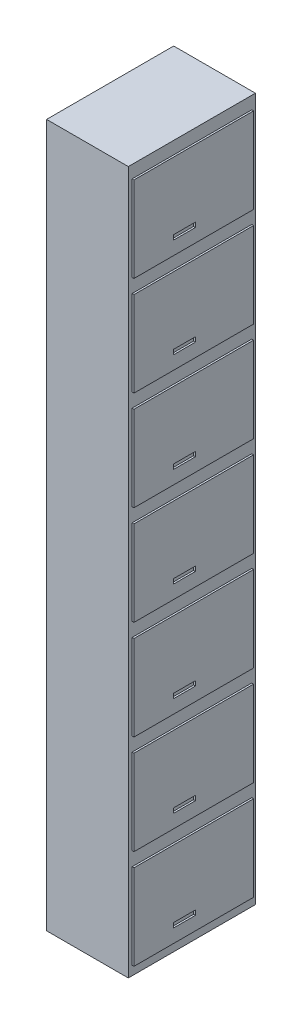
SolidWorks part; units mm, degrees
ref_plane "Front Plane" through (0, 0, 0) normal (0, 0, 1) x (1, 0, 0)
ref_plane "Top Plane" through (0, 0, 0) normal (0, 1, 0) x (1, 0, 0)
ref_plane "Right Plane" through (0, 0, 0) normal (1, 0, 0) x (0, 0, -1)
sketch "Sketch1" plane through (0, 0, 0) normal (0, 0, 1) x (1, 0, 0)
  line L0 (313.062, 4179.9863) -> (-136.938, 4179.9863)
  line L1 (-136.938, 4179.9863) -> (-136.938, 309.9863)
  line L2 (-136.938, 309.9863) -> (313.062, 309.9863)
  line L5 (313.062, 309.9863) -> (313.062, 4179.9863)
  dimension "D1" = 450
  dimension "D2" = 3870
extrude "Boss-Extrude1" add sketch "Sketch1" along normal blind 700
sketch "Sketch3" plane through (313.062, 0, 0) normal (1, 0, 0) x (0, 0, -1)
  line L1 (-678.863, 359.9863) -> (-20, 359.9863)
  line L2 (-678.863, 359.9863) -> (-678.863, 829.9863)
  line L3 (-678.863, 829.9863) -> (-20, 829.9863)
  line L4 (-20, 359.9863) -> (-20, 829.9863)
  line L5 (-700, 309.9863) -> (0, 309.9863) construction
  line L6 (-678.863, 906.7588) -> (-20, 906.7588)
  line L7 (-461.6648, -2274.1108) -> (-340.5919, -2274.1108)
  line L8 (-461.6648, -2274.1108) -> (-461.6648, -2299.9132)
  line L9 (-461.6648, -2299.9132) -> (-340.5919, -2299.9132)
  line L10 (-340.5919, -2274.1108) -> (-340.5919, -2299.9132)
  line L11 (-678.863, 906.7588) -> (-678.863, 1376.7588)
  line L12 (-678.863, 1376.7588) -> (-20, 1376.7588)
  line L13 (-20, 906.7588) -> (-20, 1376.7588)
  line L14 (-461.6648, -1727.3383) -> (-340.5919, -1727.3383)
  line L15 (-461.6648, -1753.1407) -> (-340.5919, -1753.1407)
  line L16 (-461.6648, -1727.3383) -> (-461.6648, -1753.1407)
  line L17 (-340.5919, -1727.3383) -> (-340.5919, -1753.1407)
  line L18 (-678.863, 1453.5313) -> (-20, 1453.5313)
  line L19 (-678.863, 1453.5313) -> (-678.863, 1923.5313)
  line L20 (-678.863, 1923.5313) -> (-20, 1923.5313)
  line L21 (-20, 1453.5313) -> (-20, 1923.5313)
  line L26 (-678.863, 2000.3038) -> (-20, 2000.3038)
  line L27 (-678.863, 2000.3038) -> (-678.863, 2470.3038)
  line L28 (-678.863, 2470.3038) -> (-20, 2470.3038)
  line L29 (-20, 2000.3038) -> (-20, 2470.3038)
  line L36 (-678.863, 2547.0763) -> (-20, 2547.0763)
  line L37 (-678.863, 2547.0763) -> (-678.863, 3017.0763)
  line L38 (-678.863, 3017.0763) -> (-20, 3017.0763)
  line L39 (-20, 2547.0763) -> (-20, 3017.0763)
  line L44 (-678.863, 3093.8488) -> (-20, 3093.8488)
  line L45 (-678.863, 3093.8488) -> (-678.863, 3563.8488)
  line L46 (-678.863, 3563.8488) -> (-20, 3563.8488)
  line L47 (-20, 3093.8488) -> (-20, 3563.8488)
  line L48 (-461.6648, 459.7517) -> (-340.5919, 459.7517)
  line L49 (-461.6648, 433.9492) -> (-340.5919, 433.9492)
  line L50 (-461.6648, 459.7517) -> (-461.6648, 433.9492)
  line L51 (-340.5919, 459.7517) -> (-340.5919, 433.9492)
  line L52 (-678.863, 3640.6212) -> (-20, 3640.6212)
  line L53 (-678.863, 3640.6212) -> (-678.863, 4110.6212)
  line L54 (-678.863, 4110.6212) -> (-20, 4110.6212)
  line L55 (-20, 3640.6212) -> (-20, 4110.6212)
  line L56 (-461.6648, 1006.5241) -> (-340.5919, 1006.5241)
  line L57 (-461.6648, 980.7217) -> (-340.5919, 980.7217)
  line L58 (-461.6648, 1006.5241) -> (-461.6648, 980.7217)
  line L59 (-340.5919, 1006.5241) -> (-340.5919, 980.7217)
  line L64 (-461.6648, 1553.2966) -> (-340.5919, 1553.2966)
  line L65 (-461.6648, 1527.4942) -> (-340.5919, 1527.4942)
  line L66 (-461.6648, 1553.2966) -> (-461.6648, 1527.4942)
  line L67 (-340.5919, 1553.2966) -> (-340.5919, 1527.4942)
  line L72 (-461.6648, 2100.0691) -> (-340.5919, 2100.0691)
  line L73 (-461.6648, 2074.2667) -> (-340.5919, 2074.2667)
  line L74 (-461.6648, 2100.0691) -> (-461.6648, 2074.2667)
  line L75 (-340.5919, 2100.0691) -> (-340.5919, 2074.2667)
  line L80 (-461.6648, 2646.8416) -> (-340.5919, 2646.8416)
  line L81 (-461.6648, 2621.0392) -> (-340.5919, 2621.0392)
  line L82 (-461.6648, 2646.8416) -> (-461.6648, 2621.0392)
  line L83 (-340.5919, 2646.8416) -> (-340.5919, 2621.0392)
  line L88 (-461.6648, 3193.6141) -> (-340.5919, 3193.6141)
  line L89 (-461.6648, 3167.8117) -> (-340.5919, 3167.8117)
  line L90 (-461.6648, 3193.6141) -> (-461.6648, 3167.8117)
  line L91 (-340.5919, 3193.6141) -> (-340.5919, 3167.8117)
  line L96 (-461.6648, 3740.3866) -> (-340.5919, 3740.3866)
  line L97 (-461.6648, 3714.5842) -> (-340.5919, 3714.5842)
  line L98 (-461.6648, 3740.3866) -> (-461.6648, 3714.5842)
  line L99 (-340.5919, 3740.3866) -> (-340.5919, 3714.5842)
  line L116 (-678.863, 4734.1662) -> (-678.863, 5204.1662) [skipped]
  line L117 (-678.863, 5204.1662) -> (-20, 5204.1662) [skipped]
  line L118 (-20, 4734.1662) -> (-20, 5204.1662) [skipped]
  line L119 (-678.863, 5280.9387) -> (-20, 5280.9387) [skipped]
  line L120 (-678.863, 5280.9387) -> (-678.863, 5750.9387) [skipped]
  line L121 (-678.863, 5750.9387) -> (-20, 5750.9387) [skipped]
  line L122 (-20, 5280.9387) -> (-20, 5750.9387) [skipped]
  line L123 (-678.863, 5827.7112) -> (-20, 5827.7112) [skipped]
  line L124 (-678.863, 5827.7112) -> (-678.863, 6297.7112) [skipped]
  line L125 (-678.863, 6297.7112) -> (-20, 6297.7112) [skipped]
  line L126 (-20, 5827.7112) -> (-20, 6297.7112) [skipped]
  line L127 (-678.863, 6374.4837) -> (-20, 6374.4837) [skipped]
  line L128 (-678.863, 6374.4837) -> (-678.863, 6844.4837) [skipped]
  line L129 (-678.863, 6844.4837) -> (-20, 6844.4837) [skipped]
  line L130 (-20, 6374.4837) -> (-20, 6844.4837) [skipped]
  line L131 (-678.863, 6921.2562) -> (-20, 6921.2562) [skipped]
  line L132 (-678.863, 6921.2562) -> (-678.863, 7391.2562) [skipped]
  line L133 (-678.863, 7391.2562) -> (-20, 7391.2562) [skipped]
  line L134 (-20, 6921.2562) -> (-20, 7391.2562) [skipped]
  line L135 (-678.863, 7468.0286) -> (-20, 7468.0286) [skipped]
  line L136 (-678.863, 7468.0286) -> (-678.863, 7938.0286) [skipped]
  line L137 (-678.863, 7938.0286) -> (-20, 7938.0286) [skipped]
  line L138 (-20, 7468.0286) -> (-20, 7938.0286) [skipped]
  line L139 (-678.863, 4187.3937) -> (-678.863, 4657.3937) [skipped]
  line L140 (-678.863, 4657.3937) -> (-20, 4657.3937) [skipped]
  line L141 (-20, 4187.3937) -> (-20, 4657.3937) [skipped]
  line L142 (-678.863, 4734.1662) -> (-20, 4734.1662) [skipped]
  line L143 (-461.6648, 4833.9315) -> (-340.5919, 4833.9315) [skipped]
  line L144 (-461.6648, 4808.1291) -> (-340.5919, 4808.1291) [skipped]
  line L145 (-461.6648, 4833.9315) -> (-461.6648, 4808.1291) [skipped]
  line L146 (-340.5919, 4833.9315) -> (-340.5919, 4808.1291) [skipped]
  line L147 (-678.863, 4187.3937) -> (-20, 4187.3937) [skipped]
  line L148 (-461.6648, 4287.1591) -> (-340.5919, 4287.1591) [skipped]
  line L149 (-461.6648, 4261.3567) -> (-340.5919, 4261.3567) [skipped]
  line L150 (-461.6648, 4287.1591) -> (-461.6648, 4261.3567) [skipped]
  line L151 (-340.5919, 4287.1591) -> (-340.5919, 4261.3567) [skipped]
  line L152 (-461.6648, -1180.5658) -> (-340.5919, -1180.5658) [skipped]
  line L153 (-461.6648, -1206.3682) -> (-340.5919, -1206.3682) [skipped]
  line L154 (-461.6648, -1180.5658) -> (-461.6648, -1206.3682) [skipped]
  line L155 (-340.5919, -1180.5658) -> (-340.5919, -1206.3682) [skipped]
  line L156 (-461.6648, -633.7933) -> (-340.5919, -633.7933) [skipped]
  line L157 (-461.6648, -659.5957) -> (-340.5919, -659.5957) [skipped]
  line L158 (-461.6648, -633.7933) -> (-461.6648, -659.5957) [skipped]
  line L159 (-340.5919, -633.7933) -> (-340.5919, -659.5957) [skipped]
  line L160 (-461.6648, -87.0208) -> (-340.5919, -87.0208) [skipped]
  line L161 (-461.6648, -112.8232) -> (-340.5919, -112.8232) [skipped]
  line L162 (-461.6648, -87.0208) -> (-461.6648, -112.8232) [skipped]
  line L163 (-340.5919, -87.0208) -> (-340.5919, -112.8232) [skipped]
  dimension "D1" = 470
  dimension "D3" = 50
  dimension "D4" = 14
extrude "Boss-Extrude3" add sketch "Sketch3" along normal blind 10
